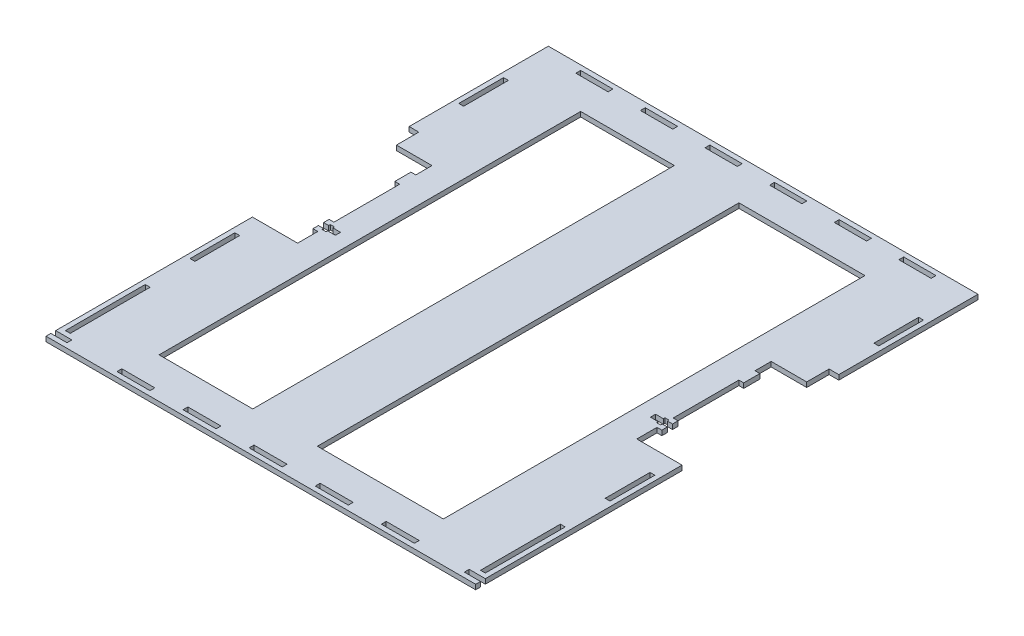
SolidWorks part; units mm, degrees
ref_plane "Front Plane" through (0, 0, 0) normal (0, 0, 1) x (1, 0, 0)
ref_plane "Top Plane" through (0, 0, 0) normal (0, 1, 0) x (1, 0, 0)
ref_plane "Right Plane" through (0, 0, 0) normal (1, 0, 0) x (0, 0, -1)
sketch "Sketch1" plane through (0, 0, 0) normal (0, 1, 0) x (1, 0, 0)
  line L0 (-127, 149.5) -> (-127, 155.5) construction
  line L1 (-133, -155.5) -> (133, -155.5)
  line L2 (-133, -155.5) -> (-133, 155.5)
  line L3 (-133, 155.5) -> (133, 155.5)
  line L4 (133, -155.5) -> (133, 155.5)
  line L5 (-133, -155.5) -> (133, 155.5) construction
  line L6 (-133, 155.5) -> (133, -155.5) construction
  line L7 (-130, -152.5) -> (130, -152.5) construction
  line L8 (-130, -152.5) -> (-130, 152.5) construction
  line L9 (-130, 152.5) -> (130, 152.5) construction
  line L10 (130, -152.5) -> (130, 152.5) construction
  line L11 (-130, -152.5) -> (130, 152.5) construction
  line L12 (-130, 152.5) -> (130, -152.5) construction
  line L13 (-127, -149.5) -> (127, -149.5) construction
  line L14 (-127, -149.5) -> (-127, 149.5) construction
  line L15 (-127, 149.5) -> (127, 149.5) construction
  line L16 (127, -149.5) -> (127, 149.5) construction
  line L17 (-127, -149.5) -> (127, 149.5) construction
  line L18 (-127, 149.5) -> (127, -149.5) construction
  line L19 (-127, 149.5) -> (-133, 149.5) construction
  line L20 (-130, 152.5) -> (-110, 152.5) construction
  line L21 (-110, 149.5) -> (-90, 149.5)
  line L22 (-110, 149.5) -> (-110, 152.5)
  line L23 (-110, 152.5) -> (-90, 152.5)
  line L24 (-90, 149.5) -> (-90, 152.5)
  line L25 (-110, 149.5) -> (-90, 152.5) construction
  line L26 (-110, 152.5) -> (-90, 149.5) construction
  line L27 (-30, 149.5) -> (-10, 149.5)
  line L28 (-30, 149.5) -> (-30, 152.5)
  line L29 (-30, 152.5) -> (-10, 152.5)
  line L30 (-10, 149.5) -> (-10, 152.5)
  line L31 (-30, 149.5) -> (-10, 152.5) construction
  line L32 (-30, 152.5) -> (-10, 149.5) construction
  line L33 (-70, 149.5) -> (-50, 149.5)
  line L34 (-70, 149.5) -> (-70, 152.5)
  line L35 (-70, 152.5) -> (-50, 152.5)
  line L36 (-50, 149.5) -> (-50, 152.5)
  line L37 (-70, 149.5) -> (-50, 152.5) construction
  line L38 (-70, 152.5) -> (-50, 149.5) construction
  line L39 (10, 149.5) -> (30, 149.5)
  line L40 (10, 149.5) -> (10, 152.5)
  line L41 (10, 152.5) -> (30, 152.5)
  line L42 (30, 149.5) -> (30, 152.5)
  line L43 (10, 149.5) -> (30, 152.5) construction
  line L44 (10, 152.5) -> (30, 149.5) construction
  line L45 (50, 149.5) -> (70, 149.5)
  line L46 (50, 149.5) -> (50, 152.5)
  line L47 (50, 152.5) -> (70, 152.5)
  line L48 (70, 149.5) -> (70, 152.5)
  line L49 (50, 149.5) -> (70, 152.5) construction
  line L50 (50, 152.5) -> (70, 149.5) construction
  line L51 (90, 149.5) -> (110, 149.5)
  line L52 (90, 149.5) -> (90, 152.5)
  line L53 (90, 152.5) -> (110, 152.5)
  line L54 (110, 149.5) -> (110, 152.5)
  line L55 (90, 149.5) -> (110, 152.5) construction
  line L56 (90, 152.5) -> (110, 149.5) construction
  line L57 (-90, 152.5) -> (-70, 152.5) construction
  line L58 (-50, 152.5) -> (-30, 152.5) construction
  line L59 (-10, 152.5) -> (10, 152.5) construction
  line L60 (30, 152.5) -> (50, 152.5) construction
  line L61 (70, 152.5) -> (90, 152.5) construction
  line L62 (110, 152.5) -> (130, 152.5) construction
  line L63 (10.2307, -149.5) -> (30.6922, -149.5) construction
  line L64 (-10.2308, -152.5) -> (10.2307, -152.5)
  line L65 (-10.2308, -152.5) -> (-10.2308, -149.5)
  line L66 (-10.2308, -149.5) -> (10.2307, -149.5)
  line L67 (10.2307, -152.5) -> (10.2307, -149.5)
  line L68 (-10.2308, -152.5) -> (10.2307, -149.5) construction
  line L69 (-10.2308, -149.5) -> (10.2307, -152.5) construction
  line L70 (30.6922, -152.5) -> (51.1537, -152.5)
  line L71 (30.6922, -152.5) -> (30.6922, -149.5)
  line L72 (30.6922, -149.5) -> (51.1537, -149.5)
  line L73 (51.1537, -152.5) -> (51.1537, -149.5)
  line L74 (30.6922, -152.5) -> (51.1537, -149.5) construction
  line L75 (30.6922, -149.5) -> (51.1537, -152.5) construction
  line L76 (92.0767, -152.5) -> (71.6152, -152.5)
  line L77 (92.0767, -152.5) -> (92.0767, -149.5)
  line L78 (92.0767, -149.5) -> (71.6152, -149.5)
  line L79 (71.6152, -152.5) -> (71.6152, -149.5)
  line L80 (92.0767, -152.5) -> (71.6152, -149.5) construction
  line L81 (92.0767, -149.5) -> (71.6152, -152.5) construction
  line L82 (-51.1538, -152.5) -> (-30.6923, -152.5)
  line L83 (-51.1538, -152.5) -> (-51.1538, -149.5)
  line L84 (-51.1538, -149.5) -> (-30.6923, -149.5)
  line L85 (-30.6923, -152.5) -> (-30.6923, -149.5)
  line L86 (-51.1538, -152.5) -> (-30.6923, -149.5) construction
  line L87 (-51.1538, -149.5) -> (-30.6923, -152.5) construction
  line L88 (-92.0768, -152.5) -> (-71.6153, -152.5)
  line L89 (-92.0768, -152.5) -> (-92.0768, -149.5)
  line L90 (-92.0768, -149.5) -> (-71.6153, -149.5)
  line L91 (-71.6153, -152.5) -> (-71.6153, -149.5)
  line L92 (-92.0768, -152.5) -> (-71.6153, -149.5) construction
  line L93 (-92.0768, -149.5) -> (-71.6153, -152.5) construction
  line L94 (51.1537, -149.5) -> (71.6152, -149.5) construction
  line L95 (-10.2308, -149.5) -> (-30.6923, -149.5) construction
  line L96 (-51.1538, -149.5) -> (-71.6153, -149.5) construction
  line L97 (128.5, -97.0455) -> (128.5, -69.3182) construction
  line L98 (133, -152.5) -> (123, -152.5)
  line L99 (133, -152.5) -> (133, -149.5)
  line L100 (133, -149.5) -> (123, -149.5)
  line L101 (123, -152.5) -> (123, -149.5)
  line L102 (133, -152.5) -> (123, -149.5) construction
  line L103 (133, -149.5) -> (123, -152.5) construction
  line L104 (-133, -152.5) -> (-123, -152.5)
  line L105 (-133, -152.5) -> (-133, -149.5)
  line L106 (-133, -149.5) -> (-123, -149.5)
  line L107 (-123, -152.5) -> (-123, -149.5)
  line L108 (-133, -152.5) -> (-123, -149.5) construction
  line L109 (-133, -149.5) -> (-123, -152.5) construction
  line L110 (127, -97.0455) -> (130, -97.0455)
  line L111 (127, -97.0455) -> (127, -146.5)
  line L112 (127, -146.5) -> (130, -146.5)
  line L113 (130, -97.0455) -> (130, -146.5)
  line L114 (127, -97.0455) -> (130, -146.5) construction
  line L115 (127, -146.5) -> (130, -97.0455) construction
  line L116 (127, -41.5909) -> (130, -41.5909)
  line L117 (127, -41.5909) -> (127, -69.3182)
  line L118 (127, -69.3182) -> (130, -69.3182)
  line L119 (130, -41.5909) -> (130, -69.3182)
  line L120 (127, -41.5909) -> (130, -69.3182) construction
  line L121 (127, -69.3182) -> (130, -41.5909) construction
  line L123 (127, 97.0454) -> (130, 97.0454)
  line L124 (127, 97.0454) -> (127, 124.7727)
  line L125 (127, 124.7727) -> (130, 124.7727)
  line L126 (130, 97.0454) -> (130, 124.7727)
  line L127 (127, 97.0454) -> (130, 124.7727) construction
  line L128 (127, 124.7727) -> (130, 97.0454) construction
  line L129 (127, 69.3181) -> (127, 55.4545)
  line L130 (127, 55.4545) -> (105, 55.4545)
  line L132 (105, -27.7273) -> (133, -27.7273)
  line L134 (130, 97.0454) -> (130, 69.3181) construction
  line L135 (105, 55.4545) -> (105, 45.4545)
  line L136 (105, 45.4545) -> (108, 45.4545)
  line L137 (108, 45.4545) -> (108, 35.4545)
  line L138 (108, 35.4545) -> (105, 35.4545)
  line L139 (105, 35.4545) -> (105, -5.2273)
  line L140 (105, -5.2273) -> (108, -5.2273)
  line L141 (108, -5.2273) -> (108, -15.2273)
  line L142 (108, -15.2273) -> (105, -15.2273)
  line L143 (105, -15.2273) -> (105, -27.7273)
  line L144 (127, 69.3181) -> (133, 69.3181)
  line L145 (133, 69.3181) -> (133, -27.7273)
  line L146 (0, -773.499) -> (0, 49226.501) construction
  line L147 (-127, -146.5) -> (-130, -146.5)
  line L148 (-130, -97.0455) -> (-130, -146.5)
  line L149 (-127, -97.0455) -> (-130, -97.0455)
  line L150 (-127, -97.0455) -> (-127, -146.5)
  line L151 (-127, -69.3182) -> (-130, -69.3182)
  line L152 (-130, -41.5909) -> (-130, -69.3182)
  line L153 (-127, -41.5909) -> (-130, -41.5909)
  line L154 (-127, -41.5909) -> (-127, -69.3182)
  line L155 (-127, 124.7727) -> (-130, 124.7727)
  line L156 (-130, 97.0454) -> (-130, 124.7727)
  line L157 (-127, 97.0454) -> (-130, 97.0454)
  line L158 (-127, 97.0454) -> (-127, 124.7727)
  line L159 (-105, -15.2273) -> (-105, -27.7273)
  line L160 (-108, -15.2273) -> (-105, -15.2273)
  line L161 (-108, -5.2273) -> (-108, -15.2273)
  line L162 (-105, -5.2273) -> (-108, -5.2273)
  line L163 (-105, 35.4545) -> (-105, -5.2273)
  line L164 (-108, 35.4545) -> (-105, 35.4545)
  line L165 (-108, 45.4545) -> (-108, 35.4545)
  line L166 (-105, 45.4545) -> (-108, 45.4545)
  line L167 (-105, 55.4545) -> (-105, 45.4545)
  line L168 (-127, 55.4545) -> (-105, 55.4545)
  line L169 (-127, 69.3181) -> (-127, 55.4545)
  line L170 (-127, 69.3181) -> (-133, 69.3181)
  line L171 (-133, 69.3181) -> (-133, -27.7273)
  line L172 (-105, -27.7273) -> (-133, -27.7273)
  line L174 (-88, -130.5) -> (88, -130.5)
  line L175 (-88, -130.5) -> (-88, 130.5)
  line L176 (-88, 130.5) -> (88, 130.5)
  line L177 (88, -130.5) -> (88, 130.5)
  line L178 (-88, -130.5) -> (88, 130.5) construction
  line L179 (-88, 130.5) -> (88, -130.5) construction
  point P0 (0, 0)
  point P6 (0, 0)
  point P11 (0, 0)
  point P16 (-100, 151)
  point P19 (-127, 152.5)
  point P21 (-130, 149.5)
  point P25 (-20, 151)
  point P30 (-60, 151)
  point P35 (20, 151)
  point P40 (60, 151)
  point P45 (100, 151)
  point P50 (128.5, -121.7728)
  point P51 (0, -151)
  point P56 (40.923, -151)
  point P61 (81.846, -151)
  point P66 (-40.923, -151)
  point P71 (-81.846, -151)
  point P76 (-128, -151)
  point P81 (128.5, 110.9091)
  point P82 (128.5, -55.4545)
  point P88 (128, -151)
  point P145 (0, 0)
  dimension "D1" = 266
  dimension "D2" = 311
  dimension "D3" = 6
  dimension "D4" = 20.4615
  dimension "D5" = 10
  dimension "D6" = 3
  dimension "D7" = 49.4545
  dimension "D8" = 27.7273
  dimension "D9" = 24.7273
  dimension "D10" = 13.8636
  dimension "D11" = 13.8636
  dimension "D12" = 22
  dimension "D13" = 10
  dimension "D14" = 40.6818
  dimension "D15" = 10
  dimension "D16" = 3
  dimension "D17" = 25
  dimension "D18" = 45
extrude "Boss-Extrude1" add sketch "Sketch1" along normal blind 3 contours L129 L144 L4 L3 L2 L106 L107 L104 L1 L98 L101 L100 L132 L143 L142 L141 L140 L139 L138 L137 L136 L135 L130 L126 L123 L124 L125 L91 L88 L89 L90 L85 L82 L83 L84 L73 L70 L71 L72 L67 L64 L65 L66
sketch "Sketch2" plane through (0, 3, 0) normal (0, 1, 0) x (1, 0, 0)
  line L0 (-108, -5.2273) -> (-108, -15.2273) construction
  line L1 (-97.5, -11.8273) -> (-108, -11.8273)
  line L2 (-97.5, -11.8273) -> (-97.5, -8.6273)
  line L3 (-97.5, -8.6273) -> (-108, -8.6273)
  line L4 (-108, -11.8273) -> (-108, -8.6273)
  line L5 (-97.5, -11.8273) -> (-108, -8.6273) construction
  line L6 (-97.5, -8.6273) -> (-108, -11.8273) construction
  line L7 (108, -5.2273) -> (108, -15.2273) construction
  line L8 (97.5, -11.8273) -> (108, -11.8273)
  line L9 (97.5, -11.8273) -> (97.5, -8.6273)
  line L10 (97.5, -8.6273) -> (108, -8.6273)
  line L11 (108, -11.8273) -> (108, -8.6273)
  line L12 (97.5, -11.8273) -> (108, -8.6273) construction
  line L13 (97.5, -8.6273) -> (108, -11.8273) construction
  line L14 (108, -10.2273) -> (104.825, -10.2273) construction
  line L15 (104.825, -12.8273) -> (102.325, -12.8273)
  line L16 (104.825, -12.8273) -> (104.825, -7.6273)
  line L17 (104.825, -7.6273) -> (102.325, -7.6273)
  line L18 (102.325, -12.8273) -> (102.325, -7.6273)
  line L19 (104.825, -12.8273) -> (102.325, -7.6273) construction
  line L20 (104.825, -7.6273) -> (102.325, -12.8273) construction
  line L21 (-102.325, -12.8273) -> (-104.825, -12.8273)
  line L22 (-102.325, -12.8273) -> (-102.325, -7.6273)
  line L23 (-102.325, -7.6273) -> (-104.825, -7.6273)
  line L24 (-104.825, -12.8273) -> (-104.825, -7.6273)
  line L25 (-102.325, -12.8273) -> (-104.825, -7.6273) construction
  line L26 (-102.325, -7.6273) -> (-104.825, -12.8273) construction
  line L27 (-108, -10.2273) -> (-104.825, -10.2273) construction
  point P0 (-102.75, -10.2273)
  point P7 (102.75, -10.2273)
  point P14 (103.575, -10.2273)
  point P19 (-103.575, -10.2273)
  point P24 (-108, -10.2273)
  point P25 (108, -10.2273)
  dimension "D1" = 3.2
  dimension "D2" = 10.5
  dimension "D3" = 2.5
  dimension "D4" = 5.2
  dimension "D5" = 3.175
extrude "Cut-Extrude1" cut sketch "Sketch2" against normal blind 10 contours L21 L24 L23 L22 | L1 L4 L3 L2 | L15 L18 L17 L16 | L8 L11 L10 L9
sketch "Sketch4" plane through (0, 0, 0) normal (0, 1, 0) x (1, 0, 0)
  line L0 (-88, 130.5) -> (88, 130.5) construction
  line L1 (-30, -130.5) -> (10, -130.5)
  line L2 (-30, -130.5) -> (-30, 130.5)
  line L3 (-30, 130.5) -> (10, 130.5)
  line L4 (10, -130.5) -> (10, 130.5)
  line L5 (-30, -130.5) -> (10, 130.5) construction
  line L6 (-30, 130.5) -> (10, -130.5) construction
  line L7 (-88, -130.5) -> (88, -130.5) construction
  point P0 (-10, 0)
  point P7 (-5.4577, -130.5)
  dimension "D1" = 40
  dimension "D2" = 10
extrude "Boss-Extrude2" add sketch "Sketch4" along normal blind 3
